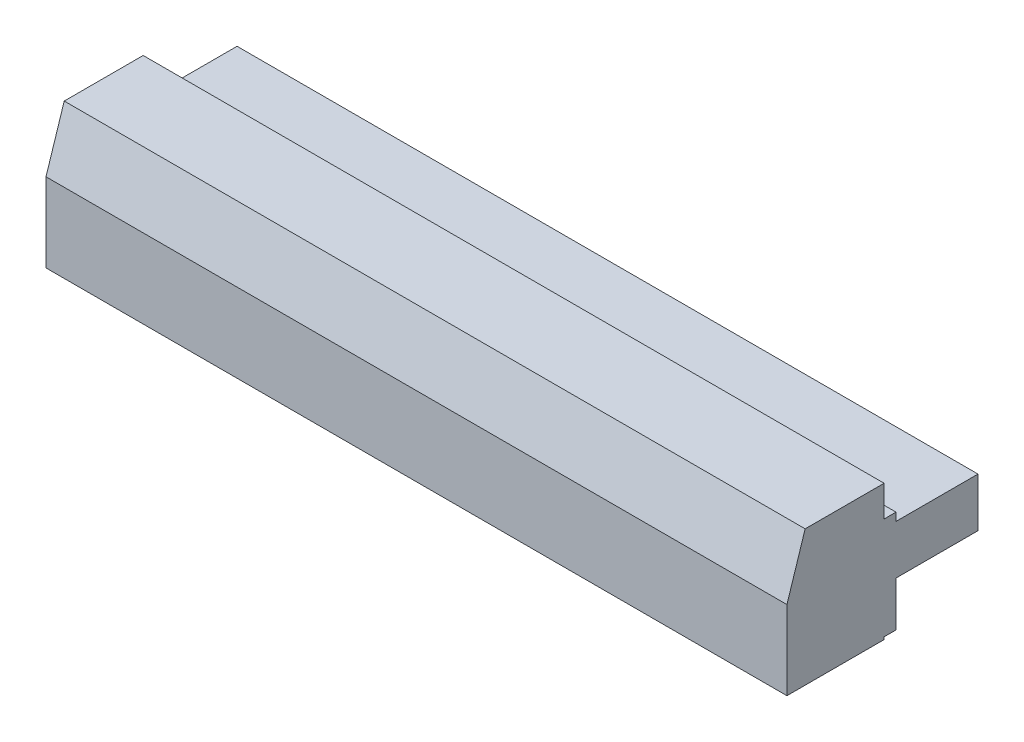
SolidWorks part; units mm, degrees
ref_plane "Front Plane" through (0, 0, 0) normal (0, 0, 1) x (1, 0, 0)
ref_plane "Top Plane" through (0, 0, 0) normal (0, 1, 0) x (1, 0, 0)
ref_plane "Right Plane" through (0, 0, 0) normal (1, 0, 0) x (0, 0, -1)
sketch "Sketch1" plane through (0, 0, 0) normal (1, 0, 0) x (0, 0, -1)
  line L0 (0, 0) -> (0, -0.2)
  line L1 (0, -0.2) -> (-8, -0.2)
  line L2 (-8, -0.2) -> (-8, 6.3)
  line L3 (-8, 6.3) -> (-6.5, 10.95)
  line L4 (-6.5, 10.95) -> (0, 10.95)
  line L5 (0, 10.95) -> (0, 8.4)
  line L6 (0, 8.4) -> (0.98, 8.4)
  line L7 (0.98, 8.4) -> (0.98, 7.74)
  line L8 (0.98, 7.74) -> (7.73, 7.74)
  line L9 (7.73, 7.74) -> (7.73, 3.7)
  line L10 (7.73, 3.7) -> (0.98, 3.7)
  line L11 (0.98, 3.7) -> (0.98, 0)
  line L12 (0.98, 0) -> (0, 0)
  dimension "D1" = 4.7
  dimension "D2" = 0.66
  dimension "D3" = 6.75
  dimension "D4" = 0.98
  dimension "D5" = 3.9
  dimension "D6" = 8.4
  dimension "D7" = 11.15
  dimension "D8" = 8
  dimension "D9" = 6.5
  dimension "D10" = 6.5
extrude "Boss-Extrude1" add sketch "Sketch1" along normal blind 61
